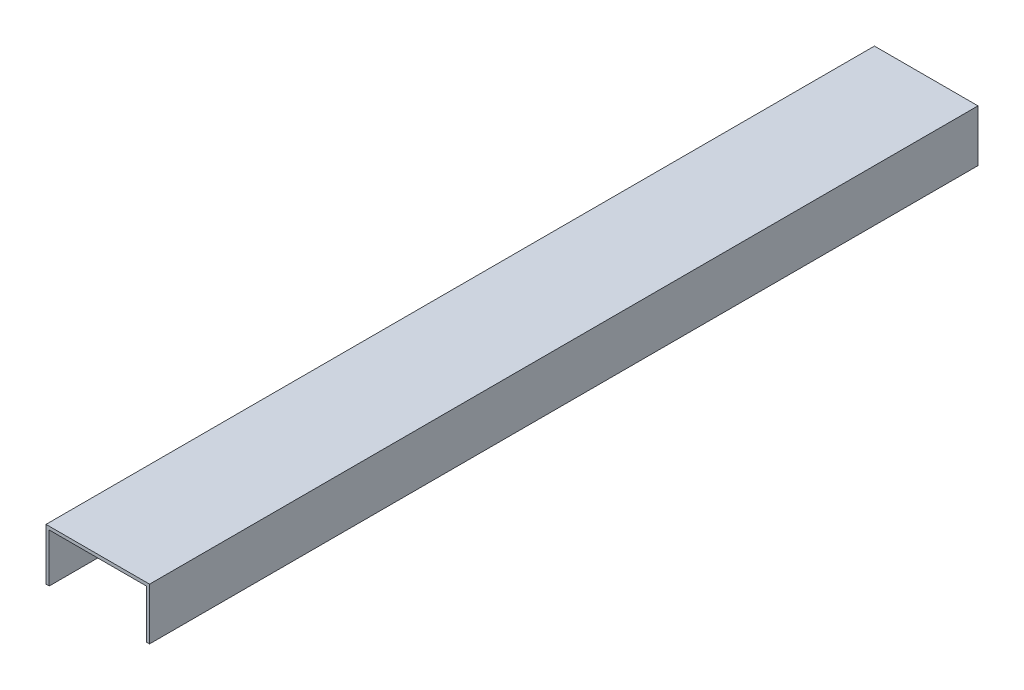
SolidWorks part; units mm, degrees
ref_plane "Front" through (0, 0, 0) normal (0, 0, 1) x (1, 0, 0)
ref_plane "Top" through (0, 0, 0) normal (0, 1, 0) x (1, 0, 0)
ref_plane "Right" through (0, 0, 0) normal (1, 0, 0) x (0, 0, -1)
sketch "Sketch1" plane through (0, 0, 0) normal (0, 0, 1) x (1, 0, 0)
  line L0 (3.175, 0) -> (3.175, 47.625)
  line L2 (0, 0) -> (0, 50.8)
  line L3 (0, 50.8) -> (101.6, 50.8)
  line L4 (101.6, 0) -> (101.6, 50.8)
  line L5 (3.175, 47.625) -> (98.425, 47.625)
  line L6 (98.425, 0) -> (98.425, 47.625)
  line L7 (0, 0) -> (3.175, 0)
  line L8 (101.6, 0) -> (98.425, 0)
  dimension "D1" = 50.8
  dimension "D2" = 101.6
  dimension "D3" = 3.175
extrude "Boss-Extrude1" add sketch "Sketch1" along normal blind 812.8
